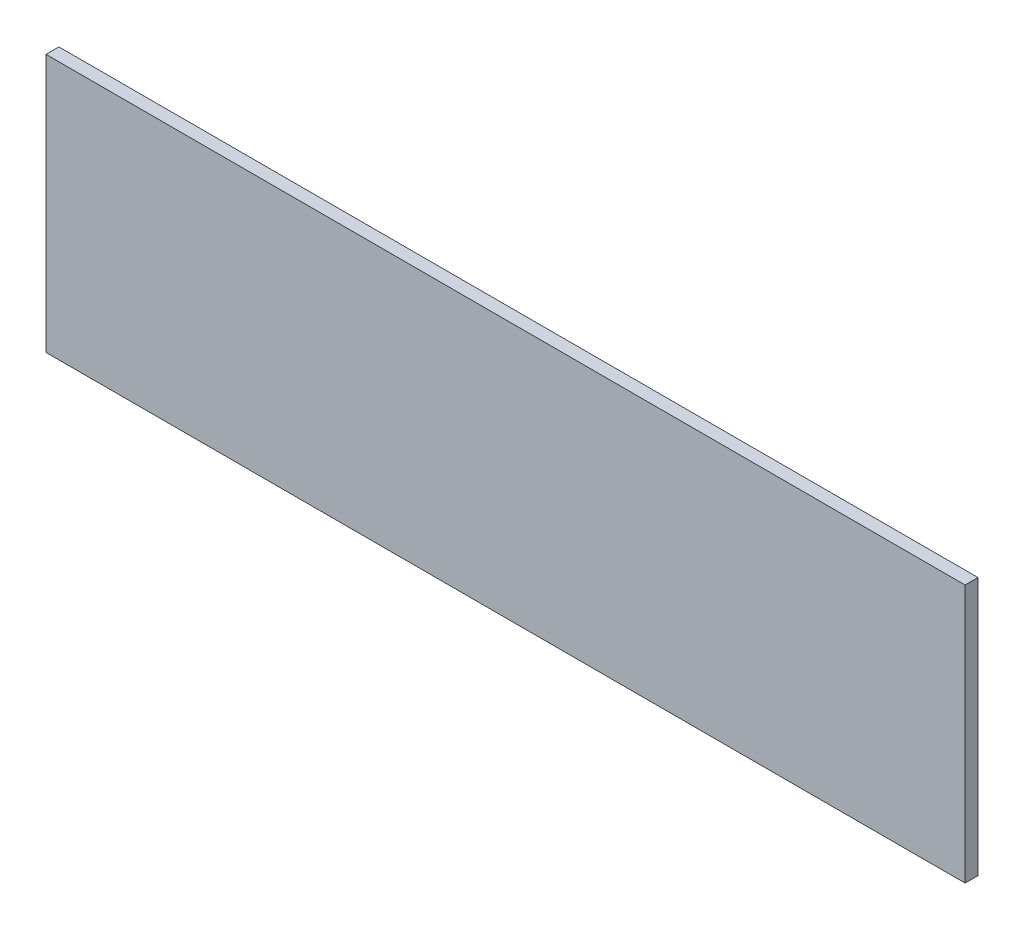
SolidWorks part; units mm, degrees
ref_plane "Plan de face" through (0, 0, 0) normal (0, 0, 1) x (1, 0, 0)
ref_plane "Plan de dessus" through (0, 0, 0) normal (0, 1, 0) x (1, 0, 0)
ref_plane "Plan de droite" through (0, 0, 0) normal (1, 0, 0) x (0, 0, -1)
sketch "Esquisse1" plane through (0, 0, 0) normal (0, 0, 1) x (1, 0, 0)
  line L1 (-356, 100) -> (0, 100)
  line L2 (-356, 100) -> (-356, 0)
  line L3 (-356, 0) -> (0, 0)
  line L4 (0, 100) -> (0, 0)
  dimension "D1" = 100
  dimension "D2" = 356
extrude "Boss.-Extru.1" add sketch "Esquisse1" along normal blind 5
